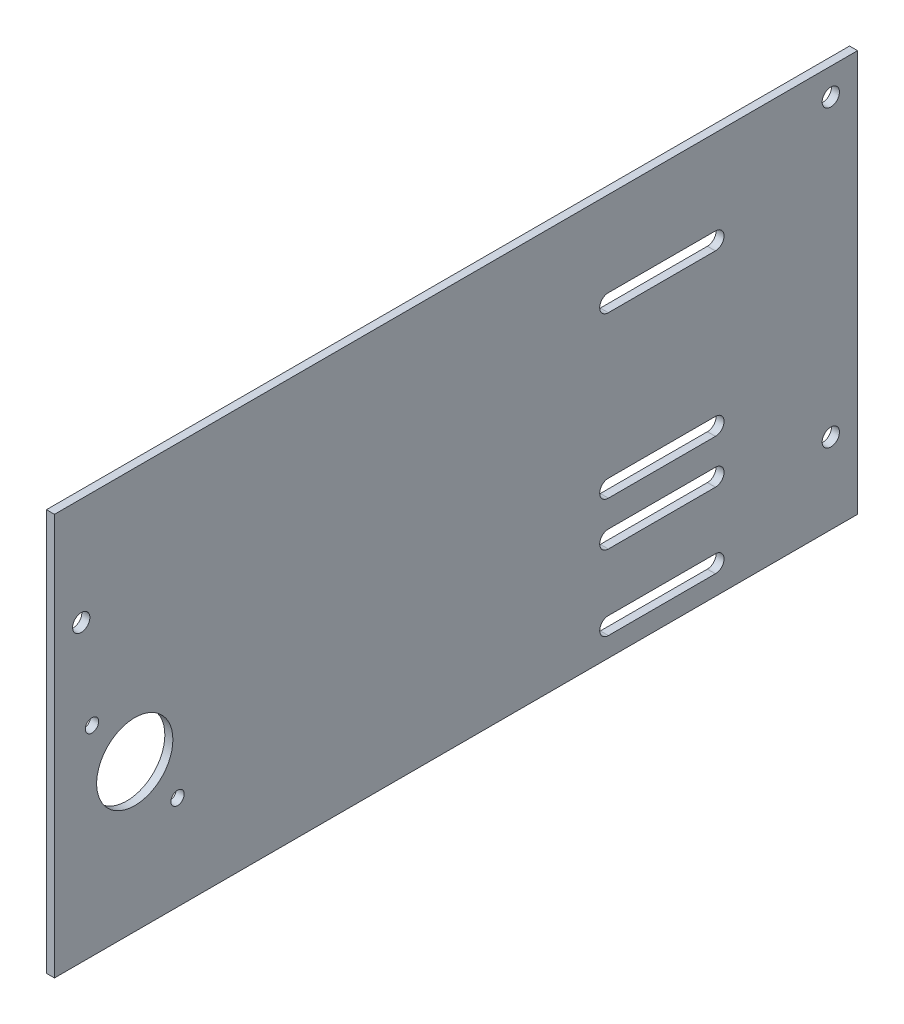
SolidWorks part; units mm, degrees
ref_plane "Front Plane" through (0, 0, 0) normal (0, 0, 1) x (1, 0, 0)
ref_plane "Top Plane" through (0, 0, 0) normal (0, 1, 0) x (1, 0, 0)
ref_plane "Right Plane" through (0, 0, 0) normal (1, 0, 0) x (0, 0, -1)
sketch "Sketch1" plane through (0, 0, 0) normal (1, 0, 0) x (0, 0, -1)
  line L1 (0, 0) -> (300, 0)
  line L2 (0, 0) -> (0, 150)
  line L3 (0, 150) -> (300, 150)
  line L4 (300, 0) -> (300, 150)
  circle A0 centre (30, 55) radius 14.235
  dimension "D1" = 300
  dimension "D5" = 28.47
  dimension "D4" = 55
  dimension "D2" = 150
  dimension "D3" = 30
extrude "Boss-Extrude1" add sketch "Sketch1" along normal blind 3
sketch "Sketch2" plane through (0, 0, 0) normal (-1, 0, 0) x (0, 0, 1)
  line L0 (-246.901, 55) -> (-206.901, 55) construction
  line L1 (-246.901, 58.225) -> (-206.901, 58.225)
  line L2 (-246.901, 51.775) -> (-206.901, 51.775)
  line L3 (-206.901, 115) -> (-246.901, 115) construction
  line L4 (-206.901, 111.77) -> (-246.901, 111.77)
  line L5 (-206.901, 118.23) -> (-246.901, 118.23)
  line L6 (-246.901, 38.55) -> (-206.901, 38.55) construction
  line L9 (-246.901, 41.775) -> (-206.901, 41.775)
  line L10 (-246.901, 35.325) -> (-206.901, 35.325)
  line L11 (-246.901, 10.55) -> (-206.901, 10.55) construction
  line L12 (-246.901, 13.775) -> (-206.901, 13.775)
  line L13 (-246.901, 7.325) -> (-206.901, 7.325)
  line L14 (0, 0) -> (-300, 0) construction
  line L15 (-300, 150) -> (0, 150) construction
  line L16 (-300, 0) -> (-300, 150) construction
  line L17 (0, 150) -> (0, 0) construction
  arc A0 (-246.901, 58.225) -> (-246.901, 51.775) centre (-246.901, 55) ccw
  arc A1 (-206.901, 51.775) -> (-206.901, 58.225) centre (-206.901, 55) ccw
  arc A3 (-206.901, 111.77) -> (-206.901, 118.23) centre (-206.901, 115) ccw
  arc A4 (-246.901, 118.23) -> (-246.901, 111.77) centre (-246.901, 115) ccw
  arc A7 (-246.901, 41.775) -> (-246.901, 35.325) centre (-246.901, 38.55) ccw
  arc A8 (-206.901, 35.325) -> (-206.901, 41.775) centre (-206.901, 38.55) ccw
  arc A9 (-246.901, 13.775) -> (-246.901, 7.325) centre (-246.901, 10.55) ccw
  arc A10 (-206.901, 7.325) -> (-206.901, 13.775) centre (-206.901, 10.55) ccw
  circle A11 centre (-290, 140) radius 3.225
  circle A12 centre (-10, 110) radius 3.225
  circle A13 centre (-290, 30) radius 3.225
  point P2 (-226.901, 55)
  point P7 (-216.901, 10.55)
  point P8 (0, 0)
  point P9 (-226.901, 115)
  point P22 (-226.901, 38.55)
  point P34 (-226.901, 10.55)
  dimension "D1" = 3.225
  dimension "D4" = 3.225
  dimension "D6" = 40
  dimension "D8" = 3.225
  dimension "D13" = 6.45
  dimension "D14" = 6.45
  dimension "D15" = 6.45
  dimension "D3" = 40
  dimension "D5" = 40
  dimension "D7" = 10
  dimension "D9" = 40
  dimension "D10" = 60
  dimension "D11" = 28
  dimension "D12" = 55
  dimension "D16" = 10
  dimension "D17" = 10
  dimension "D18" = 30
  dimension "D19" = 10
  dimension "D20" = 10
  dimension "D21" = 110
extrude "Cut-Extrude1" cut sketch "Sketch2" against normal up to next
sketch "Sketch3" plane through (3, 0, 0) normal (1, 0, 0) x (0, 0, -1)
  circle A1 centre (14.0057, 74.7318) radius 2.4892
  circle A2 centre (45.9943, 35.2682) radius 2.4892
extrude "Cut-Extrude2" cut sketch "Sketch3" against normal through all
